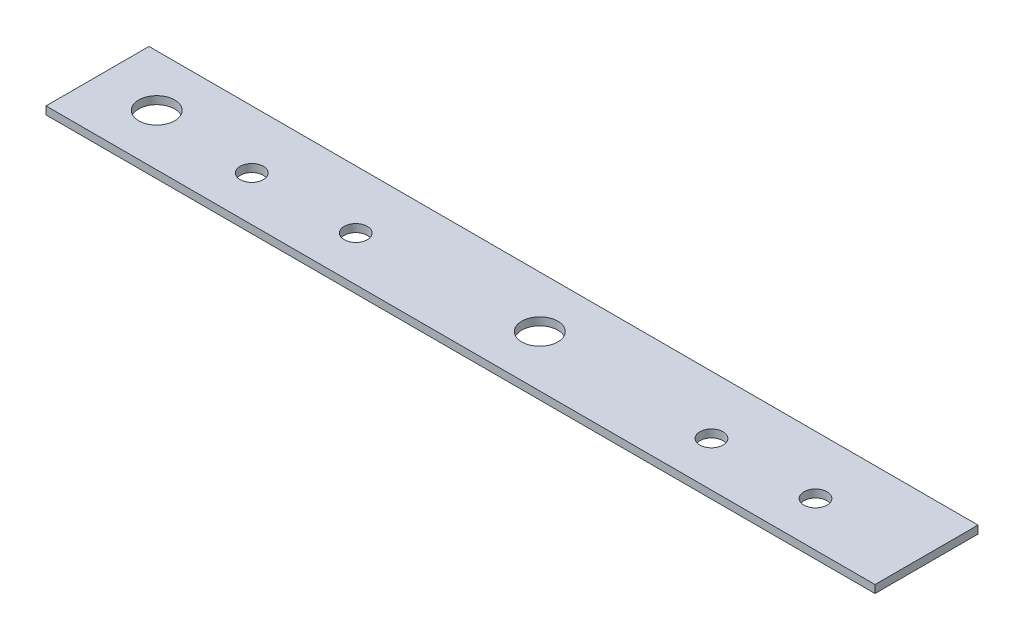
SolidWorks part; units mm, degrees
ref_plane "Front Plane" through (0, 0, 0) normal (0, 0, 1) x (1, 0, 0)
ref_plane "Top Plane" through (0, 0, 0) normal (0, 1, 0) x (1, 0, 0)
ref_plane "Right Plane" through (0, 0, 0) normal (1, 0, 0) x (0, 0, -1)
sketch "Sketch1" plane through (0, 0, 0) normal (0, 1, 0) x (1, 0, 0)
  line L1 (-40.25, 5) -> (40.25, 5)
  line L2 (-40.25, 5) -> (-40.25, -5)
  line L3 (-40.25, -5) -> (40.25, -5)
  line L4 (40.25, 5) -> (40.25, -5)
  line L5 (-40.25, 5) -> (40.25, -5) construction
  line L6 (-40.25, -5) -> (40.25, 5) construction
  circle A0 centre (-34.5, 0) radius 1.75
  circle A1 centre (-14.52, -0.65) radius 1.125
  circle A2 centre (-24.62, -0.65) radius 1.125
  circle A3 centre (2.7, 0) radius 1.75
  circle A4 centre (20.02, -0.65) radius 1.125
  circle A5 centre (30.12, -0.65) radius 1.125
  point P0 (0, 0)
  dimension "D5" = 3.5
  dimension "D6" = 2.25
  dimension "D7" = 2.25
  dimension "D10" = 2.25
  dimension "D11" = 2.25
  dimension "D13" = 3.5
  dimension "D1" = 10
  dimension "D2" = 80.5
  dimension "D3" = 10.1
  dimension "D4" = 5.75
  dimension "D8" = 9.88
  dimension "D9" = 0.65
  dimension "D12" = 10.1
  dimension "D14" = 37.2
  dimension "D15" = 17.32
extrude "Boss-Extrude1" add sketch "Sketch1" along normal mid plane 0.76
